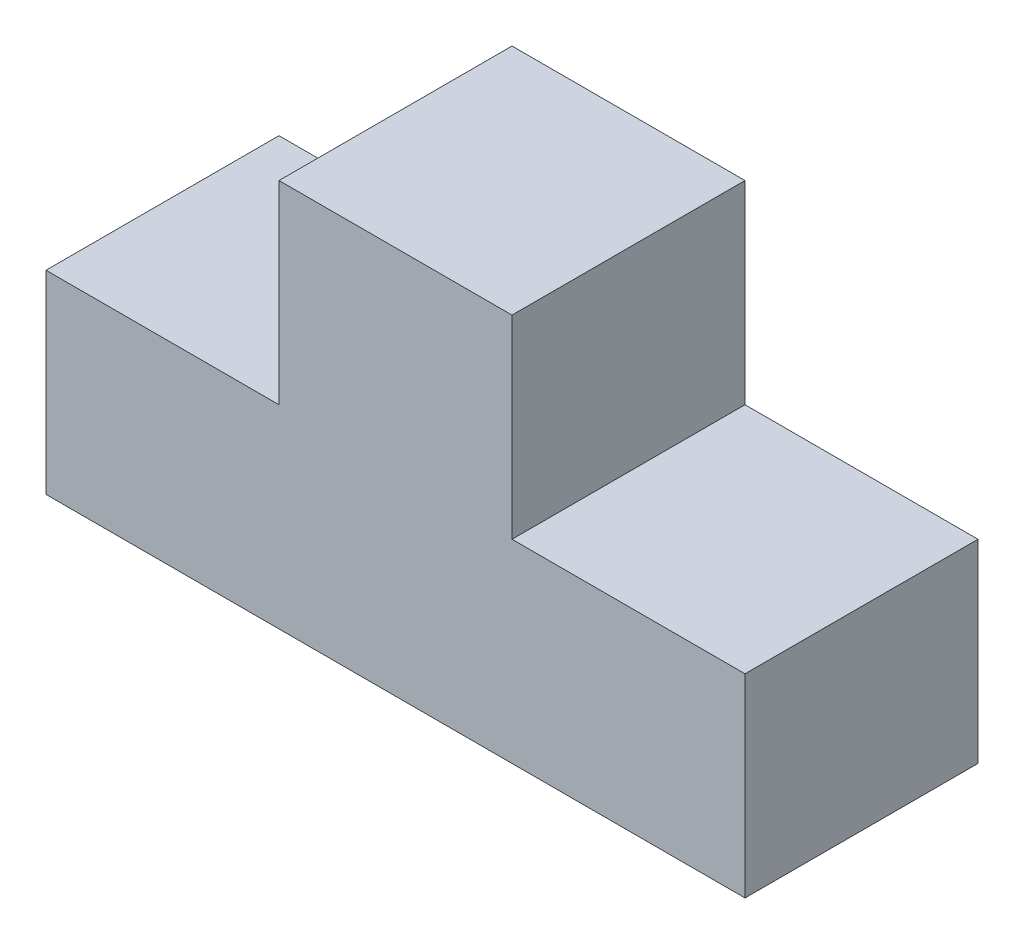
SolidWorks part; units mm, degrees
ref_plane "Front Plane" through (0, 0, 0) normal (0, 0, 1) x (1, 0, 0)
ref_plane "Top Plane" through (0, 0, 0) normal (0, 1, 0) x (1, 0, 0)
ref_plane "Right Plane" through (0, 0, 0) normal (1, 0, 0) x (0, 0, -1)
sketch "Sketch1" plane through (0, 0, 0) normal (0, 0, 1) x (1, 0, 0)
  line L0 (-45, 0) -> (45, 0)
  line L1 (45, 0) -> (45, 25)
  line L2 (45, 25) -> (15, 25)
  line L3 (15, 25) -> (15, 50)
  line L4 (15, 50) -> (-15, 50)
  line L5 (0, 50) -> (0, 0) construction
  line L6 (-15, 25) -> (-15, 50)
  line L7 (-45, 25) -> (-15, 25)
  line L8 (-45, 0) -> (-45, 25)
  dimension "D1" = 90
  dimension "D2" = 25
  dimension "D3" = 30
  dimension "D4" = 25
extrude "Boss-Extrude1" add sketch "Sketch1" along normal blind 30
